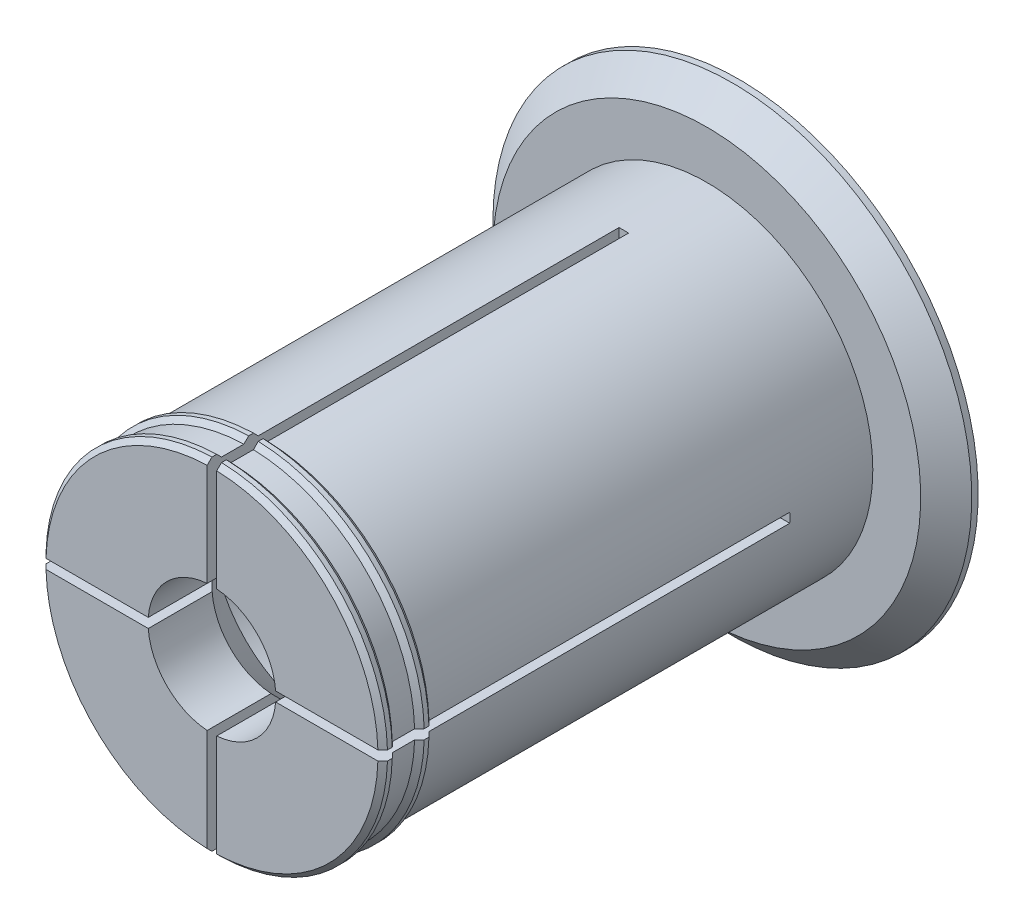
SolidWorks part; units mm, degrees
ref_plane "Front" through (0, 0, 0) normal (0, 0, 1) x (1, 0, 0)
ref_plane "Top" through (0, 0, 0) normal (0, 1, 0) x (1, 0, 0)
ref_plane "Right" through (0, 0, 0) normal (1, 0, 0) x (0, 0, -1)
sketch "Axle base sketch" plane through (0, 0, 0) normal (0, 0, 1) x (1, 0, 0)
  circle A0 centre (0, 0) radius 26
  dimension "D1" = 52
extrude "Axle" add sketch "Axle base sketch" along normal blind 77.5
sketch "Guard base" plane through (0, 0, 0) normal (0, 0, -1) x (-1, 0, 0)
  circle A0 centre (0, 0) radius 37.5
  dimension "D1" = 75
extrude "Guard" add sketch "Guard base" along normal blind 5
sketch "Inner axle hole base" plane through (0, 0, 77.5) normal (0, 0, 1) x (1, 0, 0)
  circle A0 centre (0, 0) radius 10
  dimension "D1" = 20
extrude "Inner axle hole" cut sketch "Inner axle hole base" against normal through all
sketch "Mate ring base" plane through (0, 0, 0) normal (0, 1, 0) x (1, 0, 0)
  line L0 (26, -77.5) -> (26.75, -76.75)
  line L1 (26.75, -76.75) -> (26.75, -76)
  line L2 (26.75, -76) -> (26, -75.25)
  line L3 (26.75, -76.75) -> (26.75, -77.5) construction
  line L4 (26.75, -77.5) -> (26, -77.5) construction
  line L5 (26, -75.25) -> (26, -77.5)
  line L6 (26, -77.5) -> (26, 0) construction
  line L8 (26, -71.75) -> (26.75, -71)
  line L9 (26.75, -71) -> (26.75, -70.25)
  line L10 (26.75, -70.25) -> (26, -69.5)
  line L11 (26, -69.5) -> (26, -71.75)
  dimension "D1" = 0.75
  dimension "D2" = 0.75
  dimension "D3" = 5
  dimension "D4" = 0.75
ref_axis "Center Z" through (0, 0, 0) along (0, 0, -1)
revolve "Mate rings" add sketch "Mate ring base" angle 360 about axis through (0, 0, 0) along (0, 0, -1)
sketch "Inner mass remove base" plane through (0, 0, 0) normal (1, 0, 0) x (0, 0, -1)
  line L0 (-77.5, 0) -> (-59.5, -18)
  line L1 (-59.5, -18) -> (-13, -18)
  line L2 (-13, -18) -> (5, 0)
  line L3 (5, 0) -> (-77.5, 0)
  line L4 (5, -10) -> (5, 10) construction
  line L5 (-59.5, -18) -> (-59.5, -10) construction
  line L6 (-59.5, -18) -> (-59.5, -26) construction
  line L7 (-77.5, 10) -> (-77.5, -10) construction
  point P9 (-77.5, -10)
  point P11 (-77.5, -26)
  dimension "D1" = 135
revolve "Inner mass remove" cut sketch "Inner mass remove base" angle 360 about axis through (0, 0, 0) along (0, 0, -1)
ref_point "Bend room endpoint"
sketch "Bend room base" plane through (0, 0, 77.5) normal (0, 0, 1) x (1, 0, 0)
  line L0 (0.75, -37.5) -> (0.75, 37.5)
  line L1 (0.75, 37.5) -> (-0.75, 37.5)
  line L2 (-0.75, 37.5) -> (-0.75, -37.5)
  line L3 (-0.75, -37.5) -> (0.75, -37.5)
  dimension "D1" = 0.75
  dimension "D2" = 0.75
  dimension "D3" = 37.5
  dimension "D4" = 37.5
extrude "Bend room 1" cut sketch "Bend room base" against normal up to vertex (28.9925 mm away)
pattern_circular "Bend room 2" count 2 every 90 about axis through (0, 0, 0) along (0, 0, -1) of "Bend room 1"
chamfer "Easy removal chamfer" distance 4 angle 45 1 edges at (-37.5, 0, 0)
equation "\"32_92_spool_inner_diameter\"=32"
equation "\"D1@Axle base sketch\"  = \"53_71_spool_inner_diameter\" - \"spool_inner_diameter_room\""
equation "\"spool_inner_diameter_room\"=1"
equation "\"32_92_spool_thickness\"=92"
equation "\"D1@Axle\"  = \"53_71_spool_thickness\" + \"guard_thickness\" + \"removal_room\" * 2"
equation "\"32_92_guard_diameter\"=50"
equation "\"D1@Guard base\"  = \"53_71_guard_diameter\""
equation "\"guard_thickness\"=5"
equation "\"D1@Guard\"=\"guard_thickness\""
equation "\"large_inner_axle_diameter\"=20"
equation "\"D1@Inner axle hole base\"=\"large_inner_axle_diameter\""
equation "\"mate_room\"= 0.25"
equation "\"removal_room\"= 0.75"
equation "\"small_inner_axle_diameter\"=17"
equation "\"53_55_spool_inner_diameter\"=53"
equation "\"53_55_spool_thickness\"=55"
equation "\"53_55_guard_diameter\"=75"
equation "\"D1@Mate ring base\"=\"removal_room\""
equation "\"D2@Mate ring base\"=\"removal_room\""
equation "\"D3@Mate ring base\"=\"guard_thickness\""
equation "\"D4@Mate ring base\"=\"removal_room\""
equation "\"D1@Bend room base\" = \"removal_room\""
equation "\"D2@Bend room base\"=\"removal_room\""
equation "\"D3@Bend room base\"  = \"53_71_guard_diameter\" / 2"
equation "\"D4@Bend room base\" = \"53_71_guard_diameter\" / 2"
equation "\"bend_room_length_multiplier\"=3"
equation "\"D1@Easy removal chamfer\"=\"guard_thickness\"-1"
equation "\"32_92_extra_spool_thickness\"=-5"
equation "\"39_92_spool_inner_diameter\"=39"
equation "\"39_92_spool_thickness\"=92"
equation "\"39_92_guard_diameter\"=60"
equation "\"52_62_spool_inner_diameter\"=52"
equation "\"52_62_spool_thickness\"=62"
equation "\"52_62_guard_diameter\"=75"
equation "\"53_71_spool_inner_diameter\"=53"
equation "\"53_71_spool_thickness\"=71"
equation "\"53_71_guard_diameter\"=75"
